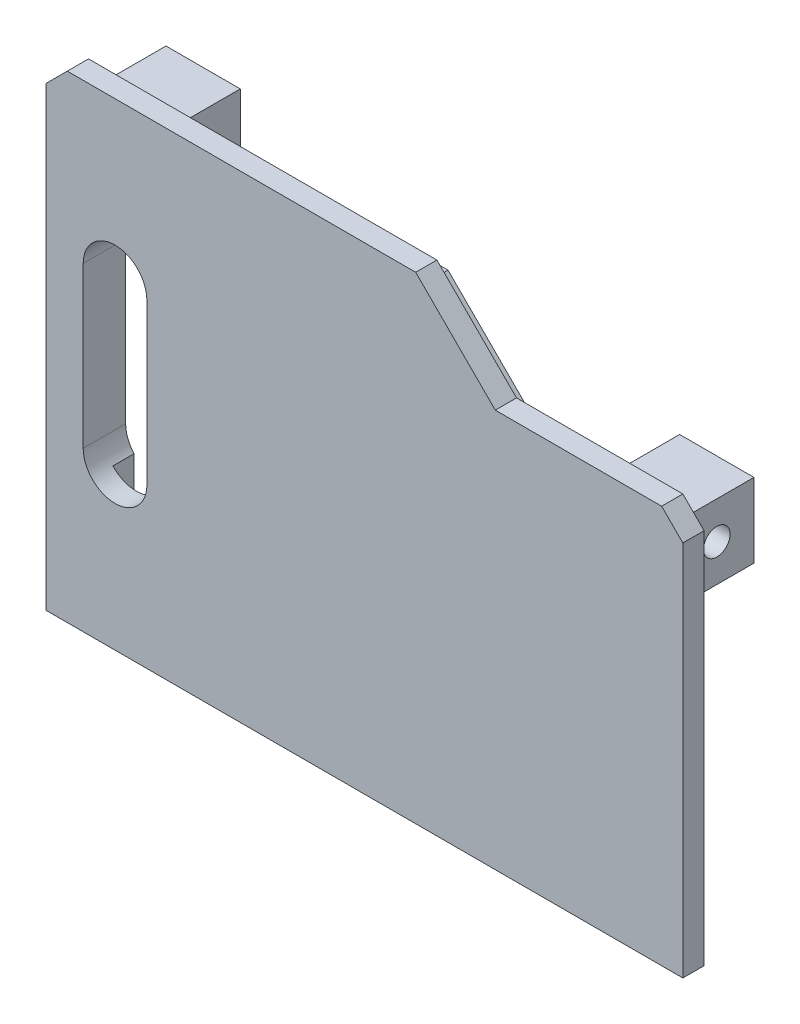
SolidWorks part; units mm, degrees
ref_plane "Спереди" through (0, 0, 0) normal (0, 0, 1) x (1, 0, 0)
ref_plane "Сверху" through (0, 0, 0) normal (0, 1, 0) x (1, 0, 0)
ref_plane "Справа" through (0, 0, 0) normal (1, 0, 0) x (0, 0, -1)
sketch "Эскиз1" plane through (0, 0, 0) normal (0, 0, 1) x (1, 0, 0)
  line L0 (-28, -20.5) -> (28, -20.5) construction
  line L1 (28, -20.5) -> (28, 13) construction
  line L2 (28, 13) -> (11.5, 13) construction
  line L3 (11.5, 13) -> (4, 20.5) construction
  line L4 (4, 20.5) -> (-28, 20.5) construction
  line L5 (-28, 20.5) -> (-28, -20.5) construction
  line L6 (-30, 20.5) -> (-28, 22.5)
  line L7 (28, 15) -> (30, 13)
  line L9 (12.3284, 15) -> (28, 15) construction
  line L10 (4.8284, 22.5) -> (12.3284, 15) construction
  line L11 (-28, 22.5) -> (4.8284, 22.5) construction
  line L12 (-28, -20.5) -> (28, -20.5) construction
  line L13 (28, -20.5) -> (28, 13) construction
  line L14 (28, 13) -> (11.5, 13) construction
  line L15 (11.5, 13) -> (4, 20.5) construction
  line L16 (4, 20.5) -> (-28, 20.5) construction
  line L17 (-28, 20.5) -> (-28, -20.5) construction
  line L18 (-30, 20.5) -> (-30, -22.5)
  line L19 (-30, -22.5) -> (30, -22.5)
  line L20 (30, -22.5) -> (30, 13)
  line L21 (12.3284, 15) -> (28, 15)
  line L22 (4.8284, 22.5) -> (12.3284, 15)
  line L23 (-28, 22.5) -> (4.8284, 22.5)
  line L24 (12.3284, 15) -> (4.8284, 22.5)
extrude "Бобышка-Вытянуть1" add sketch "Эскиз1" along normal blind 2 contours L23 L18 L19 L20 L21 L22
sketch "Эскиз4" plane through (0, 0, 0) normal (0, 0, -1) x (-1, 0, 0)
  line L0 (-28, -20.5) -> (-28, 13) construction
  line L1 (28, -20.5) -> (-28, -20.5) construction
  line L2 (28, 20.5) -> (28, -20.5) construction
  line L3 (-4, 20.5) -> (28, 20.5) construction
  line L4 (-11.5, 13) -> (-4, 20.5) construction
  line L5 (-28, 13) -> (-11.5, 13) construction
  line L6 (-28, -20.5) -> (-28, 13) construction
  line L7 (28, -20.5) -> (-28, -20.5) construction
  line L8 (28, 20.5) -> (28, -20.5) construction
  line L9 (-4, 20.5) -> (28, 20.5) construction
  line L10 (-11.5, 13) -> (-4, 20.5) construction
  line L11 (-28, 13) -> (-11.5, 13) construction
  line L12 (-27.7, -20.2) -> (-27.7, 12.7)
  line L13 (-27.7, 12.7) -> (-11.3757, 12.7)
  line L14 (-11.3757, 12.7) -> (-3.8757, 20.2)
  line L15 (-3.8757, 20.2) -> (27.7, 20.2)
  line L16 (27.7, 20.2) -> (27.7, -20.2)
  line L17 (27.7, -20.2) -> (-27.7, -20.2)
  line L18 (-25.7, 10.7) -> (-10.5473, 10.7)
  line L19 (-10.5473, 10.7) -> (-3.0473, 18.2)
  line L20 (-3.0473, 18.2) -> (25.7, 18.2)
  line L21 (25.7, 18.2) -> (25.7, -18.2)
  line L22 (25.7, -18.2) -> (-25.7, -18.2)
  line L23 (-25.7, -18.2) -> (-25.7, 10.7)
  dimension "D1" = 0.3
  dimension "D2" = 2
extrude "Бобышка-Вытянуть3" add sketch "Эскиз4" along normal blind 2
sketch "Эскиз5" plane through (27.7, 0, 0) normal (1, 0, 0) x (0, 0, -1)
  line L0 (0, 12.7) -> (7, 5.7) construction
  line L1 (0, 12.7) -> (7, 12.7)
  line L2 (0, 12.7) -> (0, 5.7)
  line L3 (0, 5.7) -> (7, 5.7)
  line L4 (7, 12.7) -> (7, 5.7)
  line L5 (0, 5.7) -> (7, 12.7) construction
  circle A0 centre (3.5, 9.2) radius 1.25
  dimension "D3" = 2.5
  dimension "D1" = 7
  dimension "D2" = 7
extrude "Бобышка-Вытянуть4" add sketch "Эскиз5" against normal blind 7
sketch "Эскиз6" plane through (-27.7, 0, 0) normal (-1, 0, 0) x (0, 0, 1)
  line L0 (-7, 20.2) -> (0, 13.2) construction
  line L1 (-7, 13.2) -> (0, 20.2) construction
  line L2 (0, 20.2) -> (-7, 20.2)
  line L3 (0, 20.2) -> (0, 13.2)
  line L4 (0, 13.2) -> (-7, 13.2)
  line L6 (-7, 20.2) -> (-7, 13.2)
  circle A0 centre (-3.5, 16.7) radius 1.25
  dimension "D3" = 2.5
  dimension "D1" = 7
  dimension "D2" = 7
extrude "Бобышка-Вытянуть5" add sketch "Эскиз6" against normal blind 7
sketch "Эскиз7" plane through (0, 0, 0) normal (0, 0, -1) x (-1, 0, 0)
  line L0 (23.5, 7.555) -> (23.5, -7.525) construction
  line L1 (23.5, 7.555) -> (23.5, -7.525) construction
  line L2 (26.5, 7.555) -> (26.5, -7.525)
  line L3 (20.5, 7.555) -> (20.5, -7.525)
  arc A0 (26.5, 7.555) -> (20.5, 7.555) centre (23.5, 7.555) ccw
  arc A1 (20.5, -7.525) -> (26.5, -7.525) centre (23.5, -7.525) ccw
  point P4 (23.5, 0.015)
  dimension "D1" = 6
extrude "Вырез-Вытянуть1" cut sketch "Эскиз7" against normal up to surface (2 mm away) and the other way blind 7 up to face at (2.1446, 7.9375, 2)
